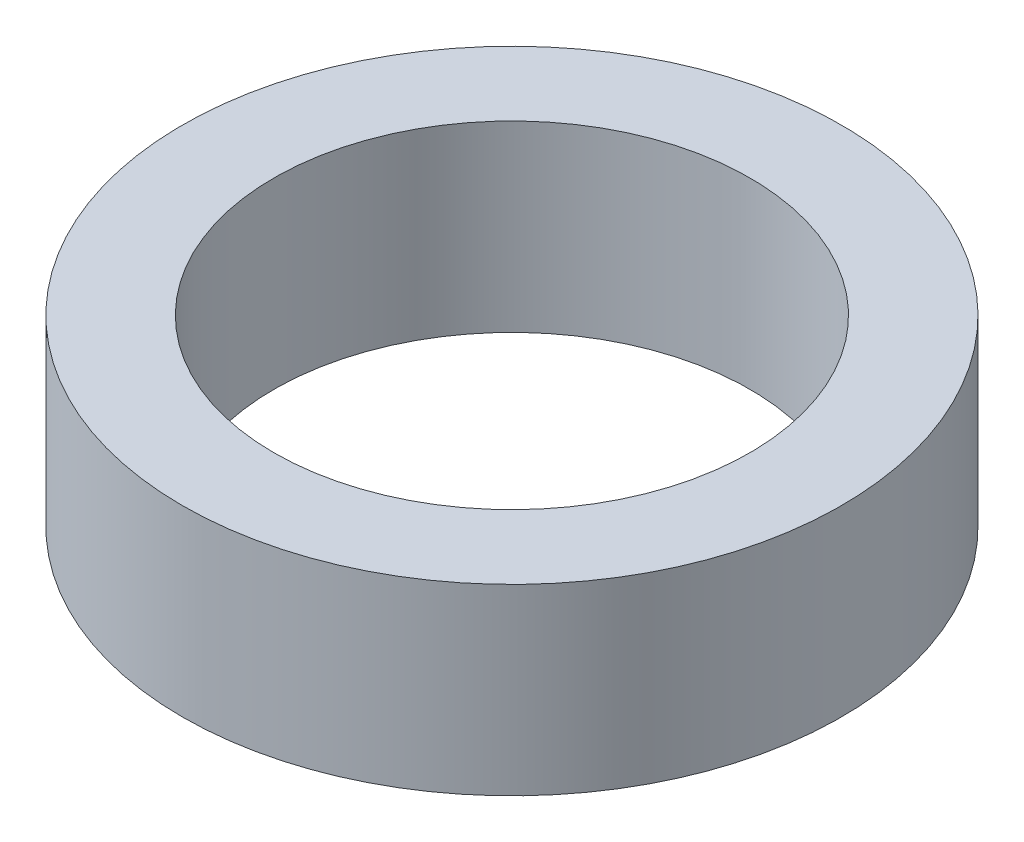
SolidWorks part; units mm, degrees
material "ABS PC"
ref_plane "Front Plane" through (0, 0, 0) normal (0, 0, 1) x (1, 0, 0)
ref_plane "Top Plane" through (0, 0, 0) normal (0, 1, 0) x (1, 0, 0)
ref_plane "Right Plane" through (0, 0, 0) normal (1, 0, 0) x (0, 0, -1)
sketch "Sketch1" plane through (0, 0, 0) normal (0, 0, 1) x (1, 0, 0)
  line L0 (18, 6.2773) -> (13, 6.2773)
  line L3 (18, 6.2773) -> (18, -3.7227)
  line L4 (18, -3.7227) -> (13, -3.7227)
  line L10 (0, 11.2232) -> (0, -13.5804) construction
  line L13 (13, 6.2773) -> (13, -3.7227)
  point P3 (15.4632, 4.4806)
  point P6 (10.4632, 7.2773)
  point P7 (10.4632, 7.0799)
  point P8 (11.4233, -3.825)
  dimension "D1" = 13
  dimension "D2" = 5
  dimension "D9" = 10
revolve "Revolve1" add sketch "Sketch1" angle 360 about L10
